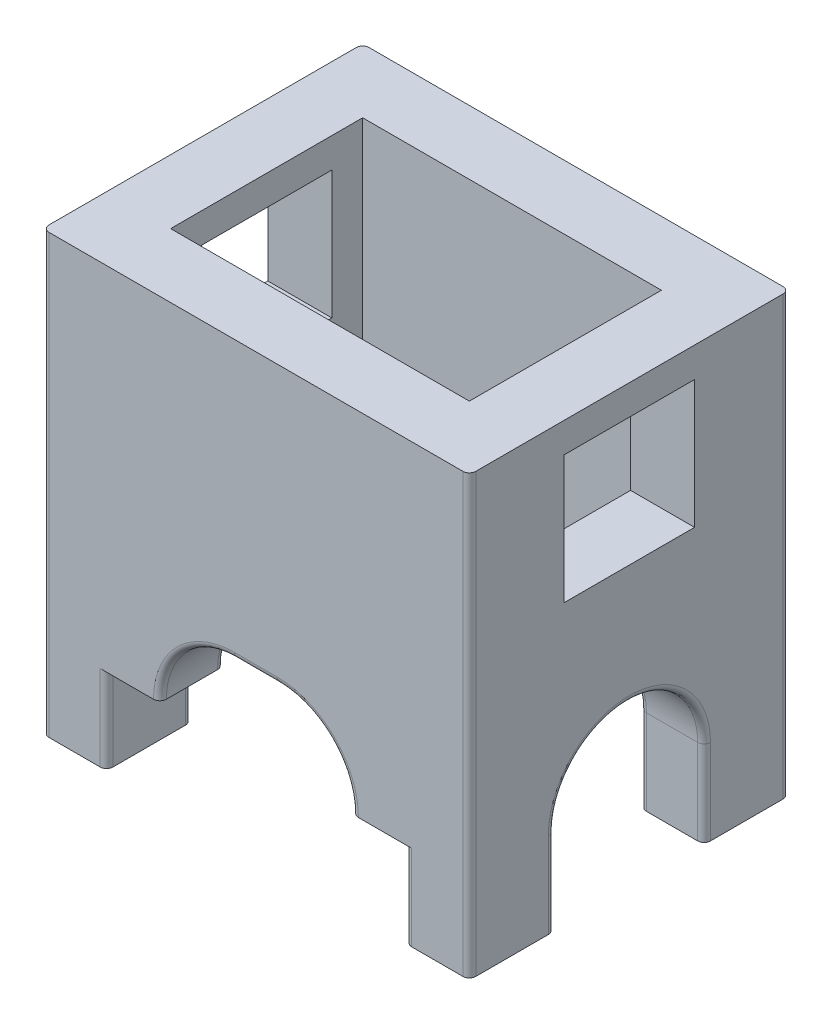
SolidWorks part; units mm, degrees
ref_plane "Спереди" through (0, 0, 0) normal (0, 0, 1) x (1, 0, 0)
ref_plane "Сверху" through (0, 0, 0) normal (0, 1, 0) x (1, 0, 0)
ref_plane "Справа" through (0, 0, 0) normal (1, 0, 0) x (0, 0, -1)
sketch "Эскиз1" plane through (0, 0, 0) normal (0, 1, 0) x (1, 0, 0)
  line L1 (7, -4.5) -> (-7, -4.5)
  line L2 (7, -4.5) -> (7, 4.5)
  line L3 (7, 4.5) -> (-7, 4.5)
  line L4 (-7, -4.5) -> (-7, 4.5)
  line L5 (7, -4.5) -> (-7, 4.5) construction
  line L6 (7, 4.5) -> (-7, -4.5) construction
  line L7 (10, -7.5) -> (-10, -7.5)
  line L8 (10, -7.5) -> (10, 7.5)
  line L9 (10, 7.5) -> (-10, 7.5)
  line L10 (-10, -7.5) -> (-10, 7.5)
  line L11 (10, -7.5) -> (-10, 7.5) construction
  line L12 (10, 7.5) -> (-10, -7.5) construction
  point P0 (0, 0)
  point P6 (0, 0)
  dimension "D1" = 9
  dimension "D2" = 14
  dimension "D3" = 15
  dimension "D4" = 20
extrude "Бобышка-Вытянуть1" add sketch "Эскиз1" against normal blind 16.5 contours L9 L10 L7 L8
sketch "Эскиз2" plane through (7, 0, 0) normal (-1, 0, 0) x (0, 0, 1)
  line L0 (0, 0) -> (0, -8.8) construction
  line L1 (4.5, 0) -> (-4.5, 0) construction
  line L3 (3.0544, -1.4) -> (-3.0544, -1.4)
  line L4 (3.0544, -1.4) -> (3.0544, -7.4)
  line L5 (3.0544, -7.4) -> (-3.0544, -7.4)
  line L6 (-3.0544, -1.4) -> (-3.0544, -7.4)
  line L7 (3.0544, -1.4) -> (-3.0544, -7.4) construction
  line L8 (3.0544, -7.4) -> (-3.0544, -1.4) construction
  point P4 (0, -4.4)
  dimension "D1" = 1.4
  dimension "D2" = 6
extrude "Вырез-Вытянуть1" cut sketch "Эскиз2" against normal through all both and the other way through all
sketch "Эскиз4" plane through (0, 0, 4.5) normal (0, 0, -1) x (-1, 0, 0)
  line L0 (-1, -16.5) -> (1, -16.5) construction
  line L1 (7, -16.5) -> (-7, -16.5) construction
  line L2 (-1, -13) -> (1, -13)
  line L3 (-1, -20) -> (1, -20)
  arc A0 (-1, -13) -> (-1, -20) centre (-1, -16.5) ccw
  arc A1 (1, -20) -> (1, -13) centre (1, -16.5) ccw
  point P4 (0, -16.5)
  dimension "D1" = 3.5
  dimension "D2" = 9
extrude "Вырез-Вытянуть2" cut sketch "Эскиз4" against normal through all both and the other way through all contours A1 L2 A0 L3
sketch "Эскиз5" plane through (-7, 0, 0) normal (1, 0, 0) x (0, 0, -1)
  line L0 (4.5, -16.5) -> (-4.5, -16.5) construction
  circle A0 centre (0, -16.5) radius 3.5
  dimension "D1" = 7
extrude "Вырез-Вытянуть3" cut sketch "Эскиз5" against normal through all both and the other way through all
sketch "Эскиз6" plane through (0, -16.5, 0) normal (0, -1, 0) x (1, 0, 0)
  line L0 (-10, 3.5) -> (-10, 7.5) construction
  line L1 (-10, -7.5) -> (-7, -7.5)
  line L2 (-10, -7.5) -> (-10, -3.5)
  line L3 (-10, -3.5) -> (-7, -3.5)
  line L4 (-7, -7.5) -> (-7, -3.5)
  line L5 (-7, 3.5) -> (-10, 3.5)
  line L6 (-7, 3.5) -> (-7, 7.5)
  line L7 (-7, 7.5) -> (-10, 7.5)
  line L8 (-10, 3.5) -> (-10, 7.5)
  line L9 (-10, 7.5) -> (-4.5, 7.5) construction
  line L11 (7, 3.5) -> (10, 3.5)
  line L12 (7, 3.5) -> (7, 7.5)
  line L13 (7, 7.5) -> (10, 7.5)
  line L14 (10, 3.5) -> (10, 7.5)
  line L15 (7, -3.5) -> (10, -3.5)
  line L16 (7, -3.5) -> (7, -7.5)
  line L17 (7, -7.5) -> (10, -7.5)
  line L18 (10, -3.5) -> (10, -7.5)
extrude "Бобышка-Вытянуть2" add sketch "Эскиз6" along normal blind 4
fillet "Скругление1" radius 0.3 4 edges at (10, -10.25, -7.5) (10, -10.25, 7.5) (-10, -10.25, 7.5) (-10, -10.25, -7.5)
fillet "Скругление2" radius 0.3 28 edges at (-3.4749, -14.0251, 7.5) (0, -13, 7.5) (-3.4749, -14.0251, 4.5) (0, -13, 4.5) (-3.4749, -14.0251, -4.5) (0, -13, -4.5) (-3.4749, -14.0251, -7.5) (0, -13, -7.5) (10, -18.5, -3.5) (10, -13, 0) (7, -18.5, -3.5) (7, -13, 0) (-10, -18.5, 3.5) (-10, -13, 0) (-7, -18.5, 3.5) (-7, -13, 0) (3.4749, -14.0251, 7.5) (3.4749, -14.0251, 4.5) (3.4749, -14.0251, -4.5) (3.4749, -14.0251, -7.5) (10, -18.5, 3.5) (7, -18.5, 3.5) (-10, -18.5, -3.5) (-7, -18.5, -3.5) (7, -18.5, -7.5) (7, -18.5, 7.5) (-7, -18.5, 7.5) (-7, -18.5, -7.5)
